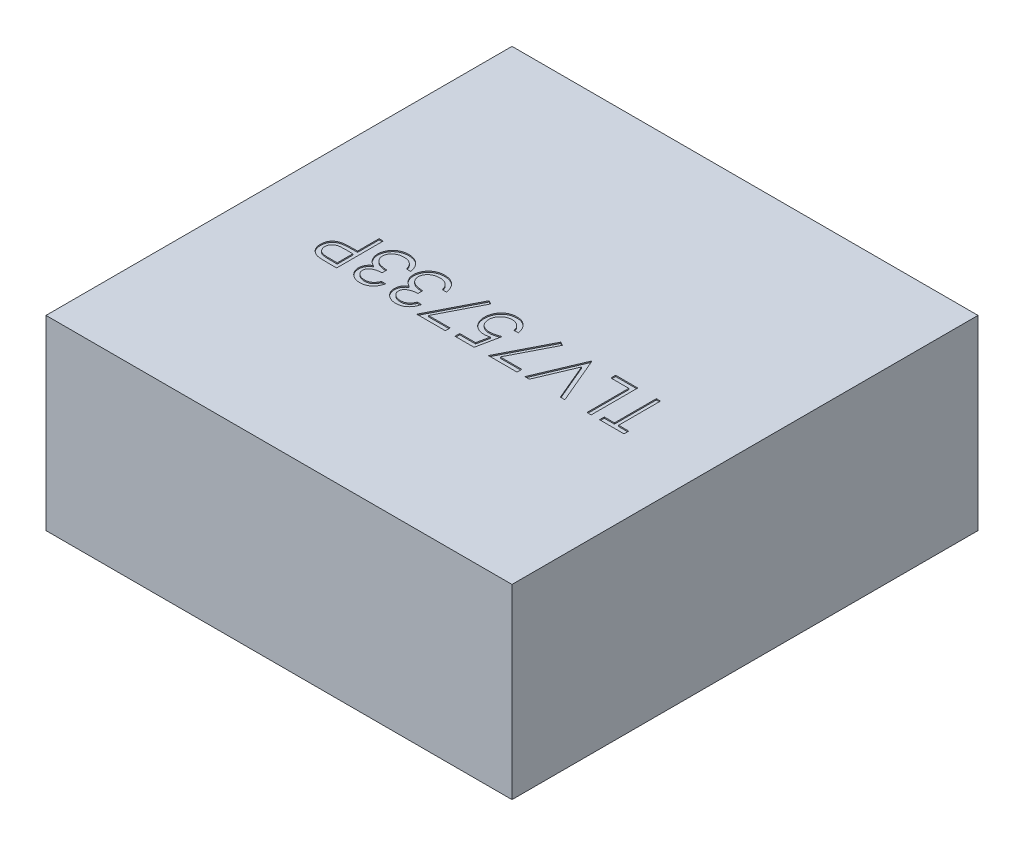
SolidWorks part; units mm, degrees
ref_plane "Front Plane" through (0, 0, 0) normal (0, 0, 1) x (1, 0, 0)
ref_plane "Top Plane" through (0, 0, 0) normal (0, 1, 0) x (1, 0, 0)
ref_plane "Right Plane" through (0, 0, 0) normal (1, 0, 0) x (0, 0, -1)
sketch "BaseS" plane through (0, 0, 0) normal (0, 1, 0) x (1, 0, 0)
  line L1 (-1, 1) -> (1, 1)
  line L2 (-1, 1) -> (-1, -1)
  line L3 (-1, -1) -> (1, -1)
  line L4 (1, 1) -> (1, -1)
  line L5 (-1, 1) -> (1, -1) construction
  line L6 (-1, -1) -> (1, 1) construction
  point P0 (0, 0)
  dimension "Dim" = 2
extrude "Base" add sketch "BaseS" along normal blind 0.8
sketch "PartNumberS" plane through (0, 0.8, 0) normal (0, 1, 0) x (1, 0, 0)
  line L0 (1, 0) -> (-1, 0) construction
  line L1 (1, -1) -> (1, 1) construction
  line L2 (-1, 1) -> (-1, -1) construction
  line L3 (-1, -1) -> (1, -1) construction
  text T0 "TLV75733P" font "Century Gothic" height 0.2
  dimension "YDim" = 1
extrude "PartNumber" cut sketch "PartNumberS" against normal blind 0.005
